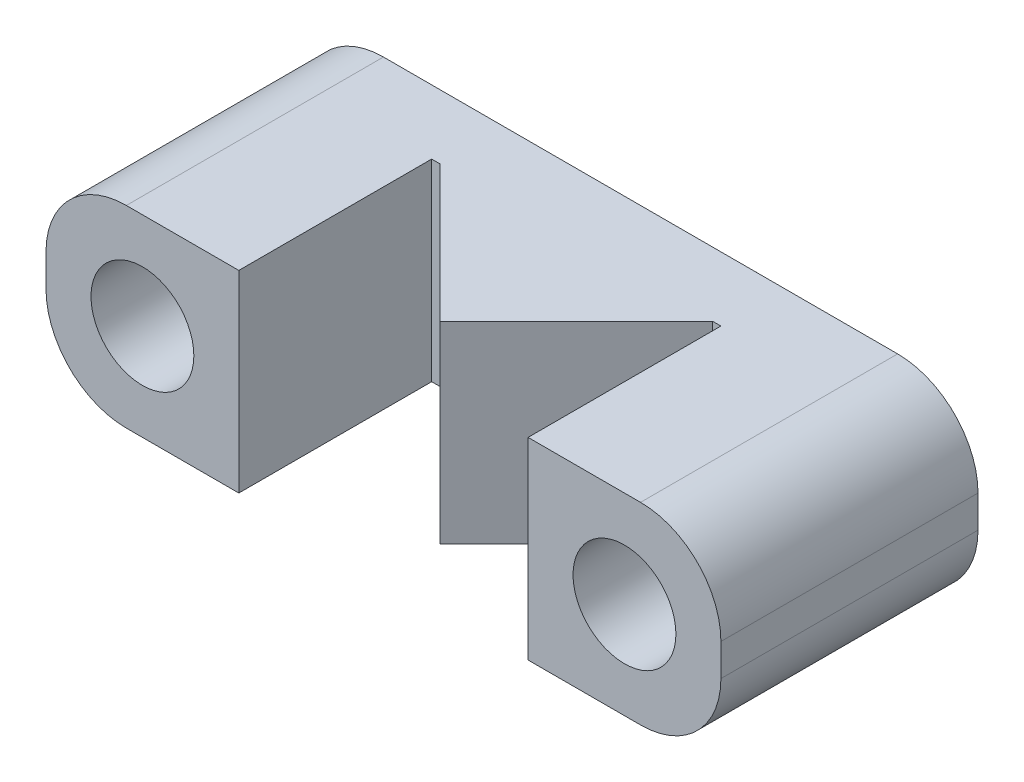
SolidWorks part; units mm, degrees
ref_plane "Front Plane" through (0, 0, 0) normal (0, 0, 1) x (1, 0, 0)
ref_plane "Top Plane" through (0, 0, 0) normal (0, 1, 0) x (1, 0, 0)
ref_plane "Right Plane" through (0, 0, 0) normal (1, 0, 0) x (0, 0, -1)
sketch "Sketch1" plane through (0, 0, 0) normal (0, 0, 1) x (1, 0, 0)
  line L1 (-0.5, 3) -> (15.5, 3)
  line L2 (-3, 0.5) -> (-3, -0.5)
  line L3 (-0.5, -3) -> (15.5, -3)
  line L4 (18, 0.5) -> (18, -0.5)
  circle A0 centre (0, 0) radius 1.6
  circle A1 centre (15, 0) radius 1.6
  arc A2 (15.5, -3) -> (18, -0.5) centre (15.5, -0.5) ccw
  arc A3 (15.5, 3) -> (18, 0.5) centre (15.5, 0.5) cw
  arc A4 (-3, -0.5) -> (-0.5, -3) centre (-0.5, -0.5) ccw
  arc A5 (-0.5, 3) -> (-3, 0.5) centre (-0.5, 0.5) ccw
  point P13 (18, 3)
  point P18 (-3, 3)
  dimension "D1" = 3.2
  dimension "D5" = 3.2
  dimension "D6" = 3
  dimension "D9" = 2.5
  dimension "D2" = 3
  dimension "D3" = 3
  dimension "D4" = 3
  dimension "D7" = 3
  dimension "D8" = 21
extrude "Boss-Extrude1" add sketch "Sketch1" along normal blind 8
sketch "Sketch2" plane through (0, -3, 0) normal (0, -1, 0) x (1, 0, 0)
  line L0 (18, 8) -> (18, 0) construction
  line L1 (3, 10.1997) -> (12, 10.1997)
  line L2 (3, 10.1997) -> (3, 2)
  line L3 (3, 2) -> (12, 2)
  line L4 (12, 10.1997) -> (12, 2)
  line L5 (-3, 8) -> (-3, 0) construction
  line L6 (-0.5, 0) -> (15.5, 0) construction
  dimension "D1" = 6
  dimension "D2" = 6
  dimension "D3" = 2
extrude "Cut-Extrude1" cut sketch "Sketch2" against normal blind 8
sketch "Sketch3" plane through (0, -3, 0) normal (0, -1, 0) x (1, 0, 0)
  line L0 (3.2574, 2) -> (7.5, 6.2426)
  line L1 (3, 2) -> (12, 2) construction
  line L2 (7.5, 6.2426) -> (11.7426, 2)
  line L3 (11.7426, 2) -> (3.2574, 2)
  line L5 (-0.5, 0) -> (15.5, 0) construction
  point P4 (10.1425, 7.1892)
  point P6 (8.9245, 7.818)
  point P7 (0, 0)
  point P10 (7.5, 0)
  point P11 (9, 6.874)
  dimension "D1" = 90
  dimension "D2" = 45
  dimension "D3" = 6
extrude "Boss-Extrude2" add sketch "Sketch3" against normal up to surface (6 mm away) up to face at (7.5, 3, 4.5)
